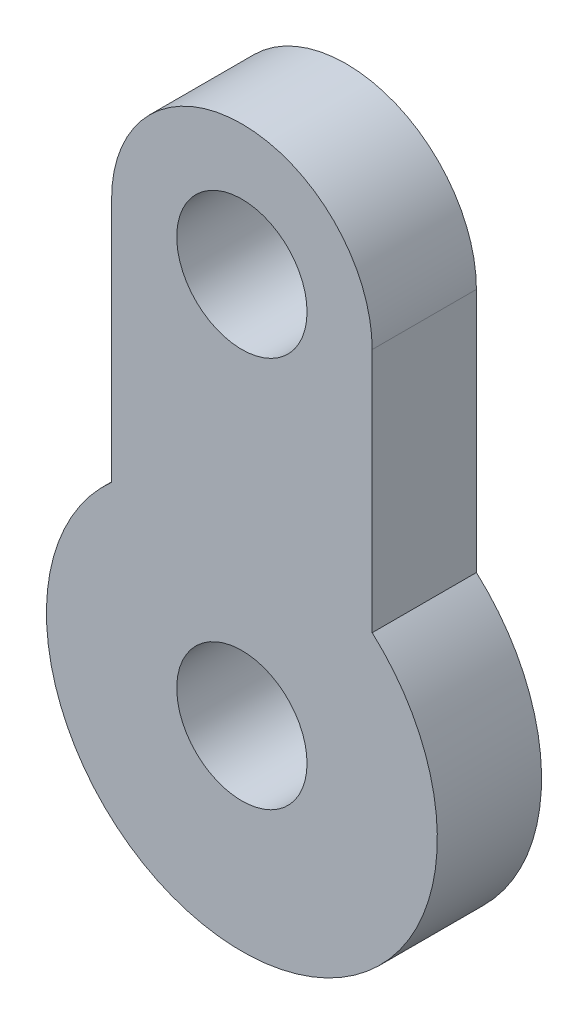
SolidWorks part; units mm, degrees
ref_plane "Front Plane" through (0, 0, 0) normal (0, 0, 1) x (1, 0, 0)
ref_plane "Top Plane" through (0, 0, 0) normal (0, 1, 0) x (1, 0, 0)
ref_plane "Right Plane" through (0, 0, 0) normal (1, 0, 0) x (0, 0, -1)
sketch "Sketch1" plane through (0, 0, 0) normal (0, 0, 1) x (1, 0, 0)
  line L0 (-6.35, 19.05) -> (-6.35, 7.0995)
  line L1 (0, 0) -> (0, 50000) construction
  line L2 (6.35, 19.05) -> (6.35, 7.0995)
  circle A0 centre (0, 0) radius 9.525 construction
  arc A1 (-6.35, 7.0995) -> (6.35, 7.0995) centre (0, 0) ccw
  arc A2 (-6.35, 19.05) -> (6.35, 19.05) centre (0, 19.05) cw
  circle A3 centre (0, 19.05) radius 3.175
  circle A4 centre (0, 0) radius 3.175
  dimension "D1" = 19.05
  dimension "D4" = 6.35
  dimension "D2" = 12.7
  dimension "D3" = 19.05
extrude "Boss-Extrude1" add sketch "Sketch1" along normal blind 5.08
